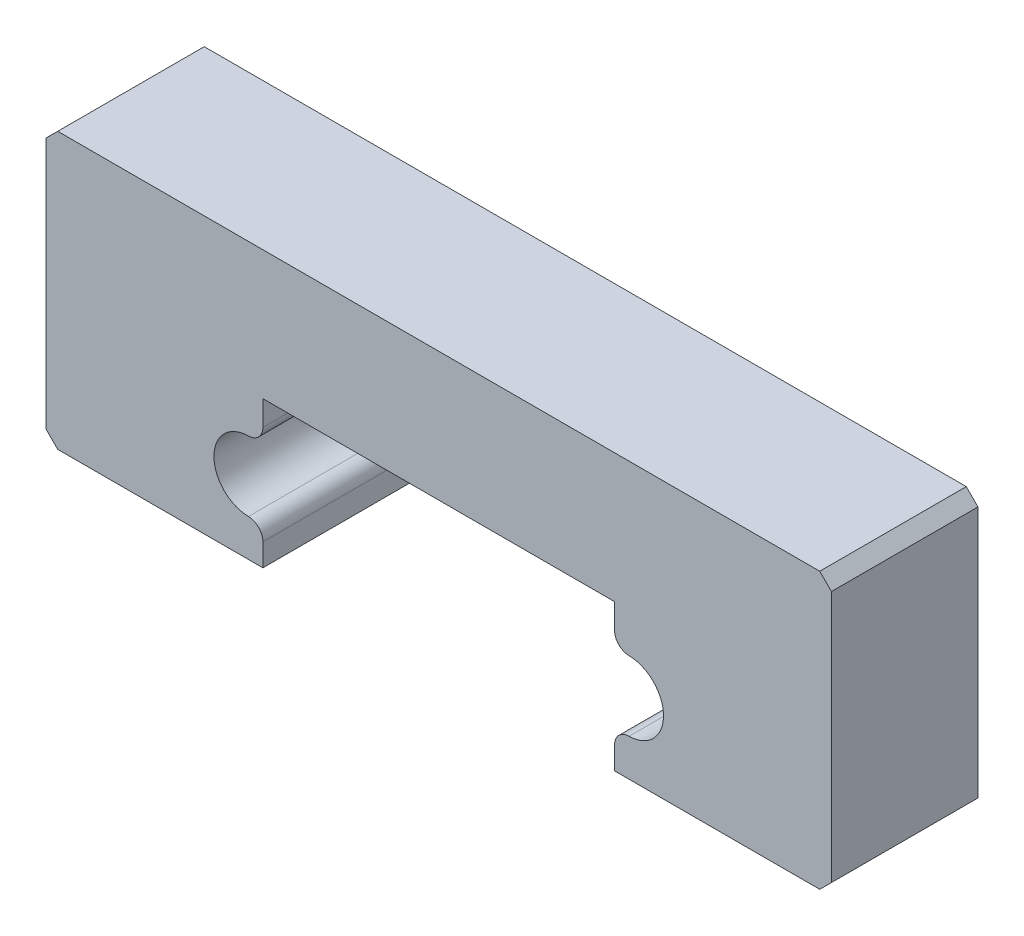
SolidWorks part; units mm, degrees
material "ABS"
ref_plane "Front Plane" through (0, 0, 0) normal (0, 0, 1) x (1, 0, 0)
ref_plane "Top Plane" through (0, 0, 0) normal (0, 1, 0) x (1, 0, 0)
ref_plane "Right Plane" through (0, 0, 0) normal (1, 0, 0) x (0, 0, -1)
sketch "Sketch1" plane through (0, 0, 0) normal (0, 0, 1) x (1, 0, 0)
  line L0 (0, 5) -> (0, -5) construction
  line L1 (-6, -5) -> (-13, -5)
  line L2 (-13, -5) -> (-13.4, -4.6)
  line L3 (-13.4, -4.6) -> (-13.4, 4)
  line L4 (-6, -5) -> (-6, -3.6289)
  line L5 (-13.4, 4) -> (-13, 4.4)
  line L6 (-13, 4.4) -> (13, 4.4)
  line L7 (6, 0) -> (-6, 0)
  line L8 (-6, 0) -> (-6, -1.4511)
  line L9 (13, -5) -> (13.4, -4.6)
  line L10 (6, 0) -> (6, -1.4511)
  line L11 (6, -5) -> (6, -3.6289)
  line L12 (13.4, 4) -> (13, 4.4)
  line L13 (13.4, -4.6) -> (13.4, 4)
  line L14 (6, -5) -> (13, -5)
  circle A0 centre (-6.48, -2.54) radius 1.19 construction
  arc A1 (-6, -1.4511) -> (-6, -3.6289) centre (-6.48, -2.54) ccw
  circle A2 centre (-4.77, -2.54) radius 0.5 construction
  arc A3 (6, -1.4511) -> (6, -3.6289) centre (6.48, -2.54) cw
  point P4 (0, 0)
  point P22 (0, 0)
  point P27 (0, 4.4)
  dimension "D9" = 2.38
  dimension "D10" = 6.48
  dimension "D11" = 2.54
  dimension "D14" = 2.54
  dimension "D15" = 4.77
  dimension "D16" = 1
  dimension "D1" = 10
  dimension "D2" = 0.4
  dimension "D3" = 0.4
  dimension "D4" = 6
  dimension "D5" = 13.4
  dimension "D6" = 0.4
  dimension "D7" = 0.4
  dimension "D8" = 9.4
  dimension "D12" = 5
  dimension "D13" = 6
extrude "Boss-Extrude1" add sketch "Sketch1" along normal blind 5
fillet "Fillet1" radius 0.5 4 edges at (6, -3.6289, 2.5) (6, -1.4511, 2.5) (-6, -1.4511, 2.5) (-6, -3.6289, 2.5)
